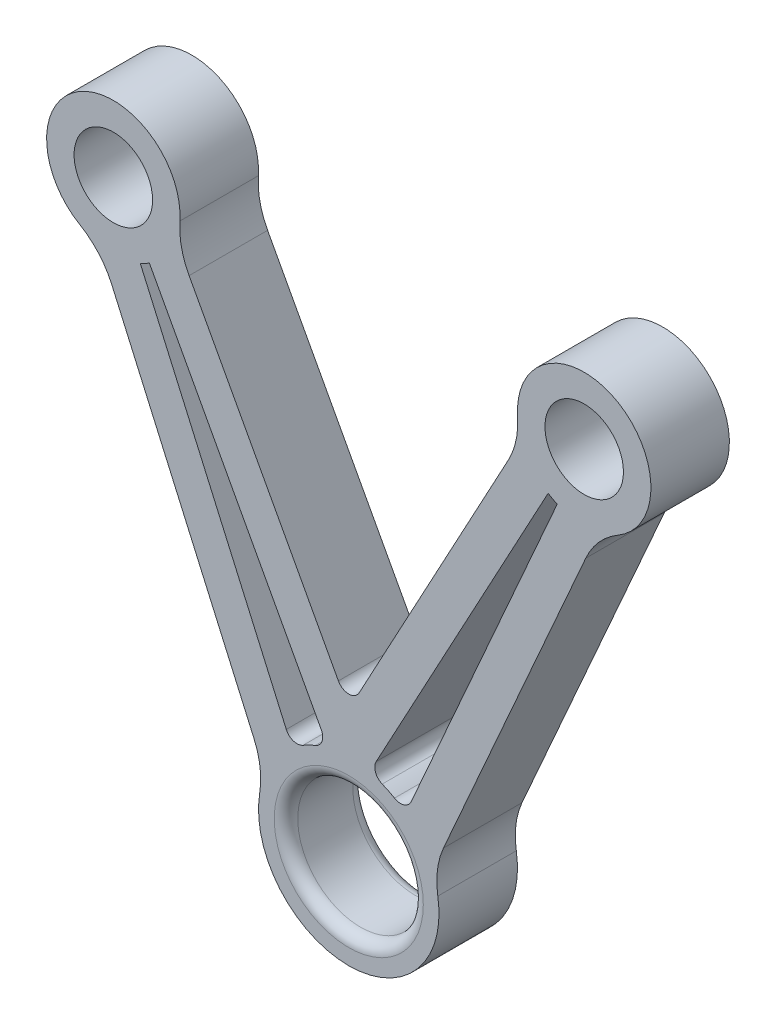
SolidWorks part; units mm, degrees
material "ABS generico"
ref_plane "Piano frontale" through (0, 0, 0) normal (0, 0, 1) x (1, 0, 0)
ref_plane "Piano superiore" through (0, 0, 0) normal (0, 1, 0) x (1, 0, 0)
ref_plane "Piano destro" through (0, 0, 0) normal (1, 0, 0) x (0, 0, -1)
sketch "Schizzo1" plane through (0, 0, 0) normal (0, 0, 1) x (1, 0, 0)
  line L0 (-30, 0) -> (30, 0) construction
  line L1 (0, -55) -> (0, 55) construction
  line L2 (55, 0) -> (-55, 0) construction
  line L3 (-31.7967, -8.3079) -> (-10.6557, -56.175)
  line L4 (22.0154, -2.9149) -> (0, -43.6683)
  line L6 (31.7967, -8.3079) -> (10.6557, -56.175)
  line L7 (-22.0154, -2.9149) -> (0, -43.6683)
  circle A0 centre (-30, 0) radius 5
  circle A1 centre (30, 0) radius 5
  arc A2 (-22.0154, -2.9149) -> (-31.7967, -8.3079) centre (-30, 0) ccw
  arc A3 (31.7967, -8.3079) -> (22.0154, -2.9149) centre (30, 0) ccw
  circle A4 centre (0, -60.5) radius 8
  arc A5 (-10.6557, -56.175) -> (10.6557, -56.175) centre (0, -60.5) ccw
  arc A6 (-10.6557, -56.175) -> (10.6557, -56.175) centre (0, -60.5) ccw
  point P6 (0, 0)
  dimension "D1" = 10
  dimension "D4" = 3.5
  dimension "D5" = 16
  dimension "D6" = 3.5
  dimension "D2" = 60
  dimension "D3" = 30
  dimension "D7" = 60.5
extrude "Estrusione-Estrusione1" add sketch "Schizzo1" along normal mid plane 10
fillet "Raccordo1" radius 10 6 edges at (22.0154, -2.9149, 0) (31.7967, -8.3079, 0) (-22.0154, -2.9149, 0) (-31.7967, -8.3079, 0) (-10.6557, -56.175, 0) (10.6557, -56.175, 0)
sketch "Schizzo2" plane through (0, 0, 5) normal (0, 0, 1) x (1, 0, 0)
  line L0 (-26.5659, -7.7754) -> (-7.2295, -51.5566)
  line L2 (25.4087, -7.1533) -> (2.6371, -49.3064)
  line L3 (26.5659, -7.7754) -> (7.2295, -51.5566)
  line L5 (-30.1991, -11.9252) -> (-12.0684, -52.9764) construction
  line L6 (20.3413, -6.0139) -> (0, -43.6683) construction
  line L7 (30.1991, -11.9252) -> (12.0684, -52.9764) construction
  line L8 (20.3413, -6.0139) -> (0, -43.6683) construction
  line L9 (-25.4087, -7.1533) -> (-2.6371, -49.3064)
  line L12 (-20.3413, -6.0139) -> (0, -43.6683) construction
  arc A0 (-26.5659, -7.7754) -> (-25.4087, -7.1533) centre (-30, 0) ccw
  arc A2 (25.4087, -7.1533) -> (26.5659, -7.7754) centre (30, 0) ccw
  arc A3 (-21.5198, -0.5794) -> (-34.2944, -7.3354) centre (-30, 0) ccw construction
  arc A4 (-11.3481, -58.6367) -> (11.3481, -58.6367) centre (0, -60.5) ccw construction
  arc A5 (34.2944, -7.3354) -> (21.5198, -0.5794) centre (30, 0) ccw construction
  arc A6 (7.2295, -51.5566) -> (2.6371, -49.3064) centre (0, -60.5) ccw
  arc A9 (-2.6371, -49.3064) -> (-7.2295, -51.5566) centre (0, -60.5) ccw
  dimension "D1" = 5
  dimension "D2" = 5
  dimension "D3" = 5
  dimension "D4" = 5
extrude "Taglio-Estrusione1" cut sketch "Schizzo2" against normal up to surface (10 mm away) up to face at (0, -23.7261, -5)
fillet "Raccordo2" radius 1.5 7 edges at (0, -43.6683, 0) (7.2295, -51.5566, 0) (2.6371, -49.3064, 0) (-2.6371, -49.3064, 0) (-7.2295, -51.5566, 0) (8, -60.5, -5) (8, -60.5, 5)
